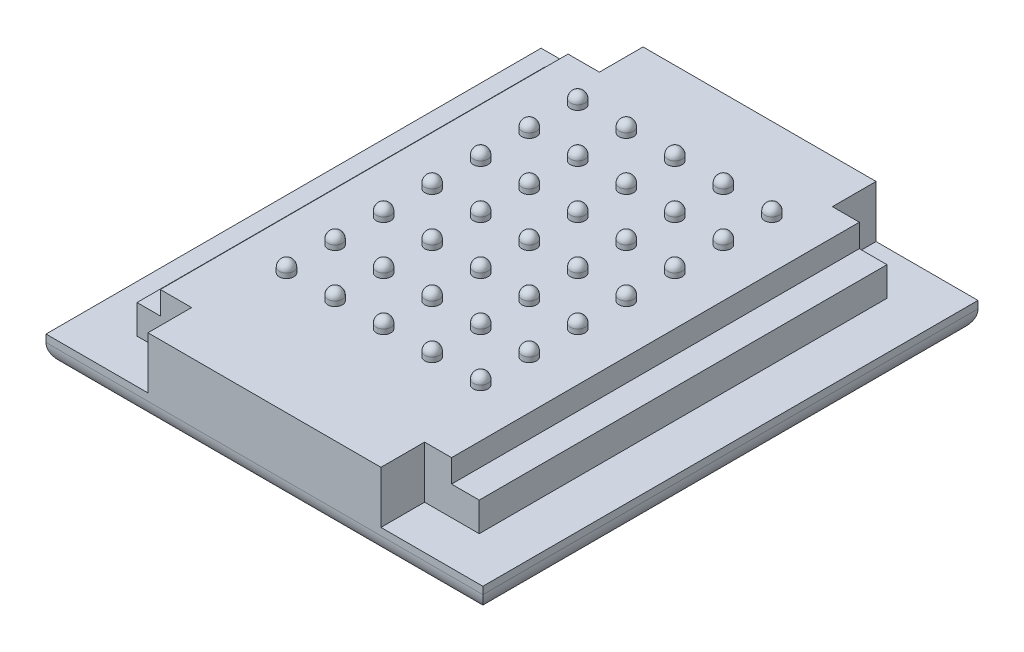
SolidWorks part; units mm, degrees
ref_plane "Front Plane" through (0, 0, 0) normal (0, 0, 1) x (1, 0, 0)
ref_plane "Top Plane" through (0, 0, 0) normal (0, 1, 0) x (1, 0, 0)
ref_plane "Right Plane" through (0, 0, 0) normal (1, 0, 0) x (0, 0, -1)
sketch "Sketch1" plane through (0, 0, 0) normal (0, 1, 0) x (1, 0, 0)
  line L1 (-19.2665, 11.2929) -> (18.8335, 11.2929)
  line L2 (-19.2665, 11.2929) -> (-19.2665, -31.8871)
  line L3 (-19.2665, -31.8871) -> (18.8335, -31.8871)
  line L4 (18.8335, 11.2929) -> (18.8335, -31.8871)
  dimension "D1" = 38.1
  dimension "D2" = 43.18
extrude "Boss-Extrude1" add sketch "Sketch1" along normal blind 2.54
sketch "Sketch2" plane through (0, 2.54, 0) normal (0, 1, 0) x (1, 0, 0)
  line L0 (18.8335, 11.2929) -> (-19.2665, 11.2929) construction
  line L1 (-15.139, 7.4829) -> (14.706, 7.4829)
  line L2 (-15.139, 7.4829) -> (-15.139, -28.0771)
  line L3 (-15.139, -28.0771) -> (14.706, -28.0771)
  line L4 (14.706, 7.4829) -> (14.706, -28.0771)
  line L5 (-19.2665, 11.2929) -> (-19.2665, -31.8871) construction
  dimension "D1" = 29.845
  dimension "D2" = 35.56
  dimension "D3" = 3.81
  dimension "D4" = 4.1275
extrude "Boss-Extrude2" add sketch "Sketch2" along normal blind 2.54
sketch "Sketch3" plane through (0, 5.08, 0) normal (0, 1, 0) x (1, 0, 0)
  line L0 (14.706, 7.4829) -> (-15.139, 7.4829) construction
  line L1 (-13.107, 7.4829) -> (12.293, 7.4829)
  line L2 (-13.107, 7.4829) -> (-13.107, -28.0771)
  line L3 (-13.107, -28.0771) -> (12.293, -28.0771)
  line L4 (12.293, 7.4829) -> (12.293, -28.0771)
  line L5 (-15.139, -28.0771) -> (14.706, -28.0771) construction
  line L6 (-15.139, 7.4829) -> (-15.139, -28.0771) construction
  dimension "D1" = 25.4
  dimension "D2" = 2.032
extrude "Boss-Extrude3" add sketch "Sketch3" along normal blind 2
sketch "Sketch4" plane through (0, 7.08, 0) normal (0, 1, 0) x (1, 0, 0)
  line L0 (-13.107, 7.4829) -> (-13.107, -28.0771) construction
  line L1 (12.293, 7.4829) -> (-13.107, 7.4829) construction
  line L2 (-8.8736, 4.7312) -> (-8.8736, 3.4612) construction
  circle A0 centre (-8.8736, 4.0962) radius 0.635
  dimension "D1" = 1.27
  dimension "D2" = 4.2333
  dimension "D3" = 3.3867
revolve "Revolve6" add sketch "Sketch4" angle 360 about L2
move or copy body "Body-Move/Copy2" bodies to move or copy 104 copy no translate (0, 0.4233, 0)
sketch "Sketch5" plane through (0, 7.08, 0) normal (0, 1, 0) x (1, 0, 0)
  line L0 (-13.107, 7.4829) -> (-13.107, -28.0771) construction
  line L2 (12.293, 7.4829) -> (-13.107, 7.4829) construction
  circle A0 centre (-8.8736, 4.0962) radius 0.635
  point P6 (-11.0393, 7.4829)
  dimension "D1" = 1.27
  dimension "D2" = 4.2333
  dimension "D3" = 3.3867
extrude "Boss-Extrude4" add sketch "Sketch5" along normal blind 0.4233 separate body
combine bodies "Combine1" operation type add bodies to combine 142 143
pattern_linear "LPattern1" count 5 spacing 4.2333 along (1, 0, 0) count 7 spacing 4.2333 along (0, 0, 1) of bodies 144
sketch "Sketch7" plane through (0, 2.54, 0) normal (0, 1, 0) x (1, 0, 0)
  line L0 (-15.139, -28.0771) -> (14.706, -28.0771) construction
  line L1 (-10.3765, -28.0771) -> (9.9435, -28.0771)
  line L2 (-10.3765, -28.0771) -> (-10.3765, -31.8871)
  line L3 (-10.3765, -31.8871) -> (9.9435, -31.8871)
  line L4 (9.9435, -28.0771) -> (9.9435, -31.8871)
  line L5 (-19.2665, -31.8871) -> (18.8335, -31.8871) construction
  line L6 (18.8335, 11.2929) -> (-19.2665, 11.2929) construction
  line L7 (-10.3765, 11.2929) -> (9.9435, 11.2929)
  line L8 (-10.3765, 11.2929) -> (-10.3765, 7.4829)
  line L9 (-10.3765, 7.4829) -> (9.9435, 7.4829)
  line L10 (9.9435, 11.2929) -> (9.9435, 7.4829)
  line L11 (14.706, 7.4829) -> (-15.139, 7.4829) construction
  line L12 (-19.2665, 11.2929) -> (-19.2665, -31.8871) construction
  point P18 (-10.3765, -29.9821)
  point P19 (9.9435, -29.9821)
  dimension "D1" = 20.32
  dimension "D2" = 8.89
  dimension "D3" = 8.89
  dimension "D4" = 20.32
extrude "Boss-Extrude5" add sketch "Sketch7" along normal up to surface (4.54 mm away) up to face at (-0.407, 7.08, 10.2971)
fillet "Fillet1" radius 1.905 4 edges at (-0.2165, 0, 31.8871) (18.8335, 0, 10.2971) (-0.2165, 0, -11.2929) (-19.2665, 0, 10.2971)
